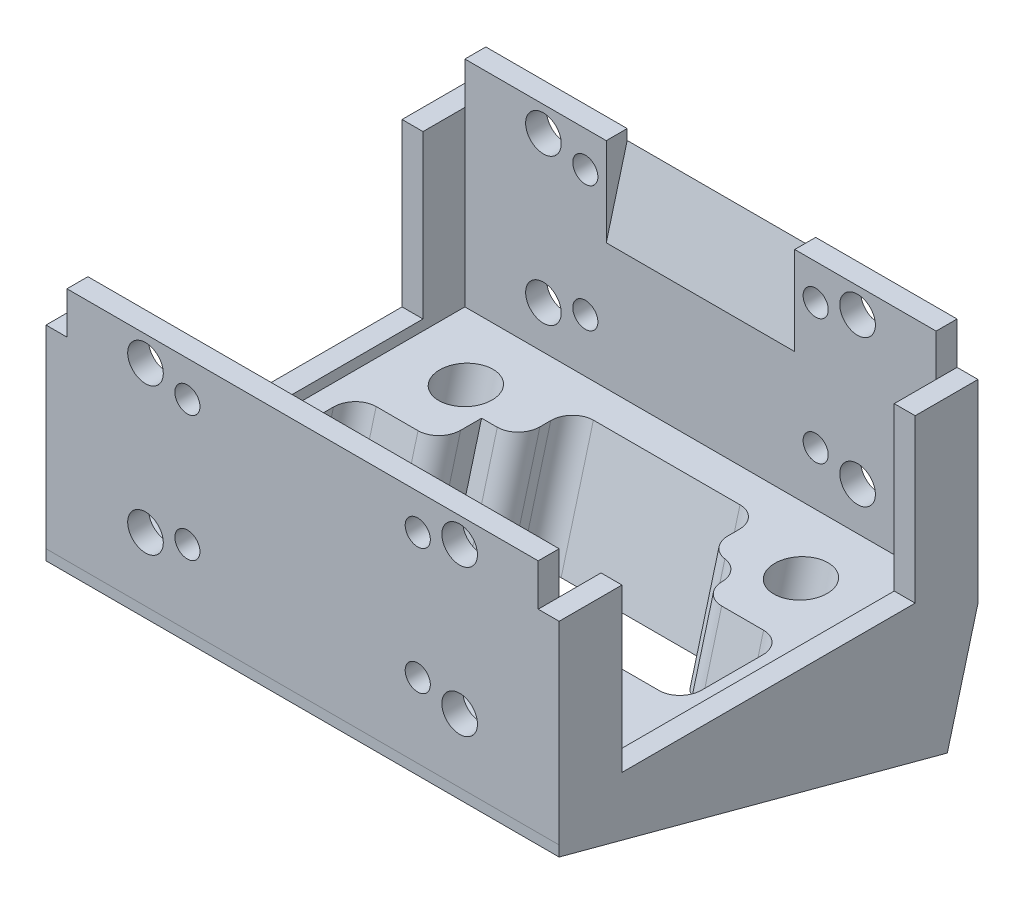
SolidWorks part; units mm, degrees
ref_plane "Front Plane" through (0, 0, 0) normal (0, 0, 1) x (1, 0, 0)
ref_plane "Top Plane" through (0, 0, 0) normal (0, 1, 0) x (1, 0, 0)
ref_plane "Right Plane" through (0, 0, 0) normal (1, 0, 0) x (0, 0, -1)
ref_plane "Plane1" through (24.5, 0, 0) normal (1, 0, 0) x (0, 0, -1)
sketch "Sketch1" plane through (24.5, 0, 0) normal (1, 0, 0) x (0, 0, -1)
  line L0 (20, 18.5) -> (-20, 18.5)
  line L1 (-20, 18.5) -> (-20, 0)
  line L2 (-20, 0) -> (-20.0017, -1)
  line L3 (-20.0017, -1) -> (17.0704, -10.9334)
  line L4 (17.0704, -10.9334) -> (20, 0)
  line L5 (20, 0) -> (20, 18.5)
extrude "Boss-Extrude1" add sketch "Sketch1" against normal blind 49
sketch "Sketch2" plane through (0, 18.5, 0) normal (0, 1, 0) x (-1, 0, 0)
  line L0 (22.5, 20) -> (22.5, 18)
  line L1 (22.5, 18) -> (-22.5, 18)
  line L2 (-22.5, 18) -> (-22.5, 20)
  line L3 (-22.5, 20) -> (22.5, 20)
extrude "Boss-Extrude2" add sketch "Sketch2" along normal blind 4
sketch "Sketch3" plane through (0, 18.5, 0) normal (0, 1, 0) x (-1, 0, 0)
  line L0 (22.5, -18) -> (22.5, -20)
  line L1 (22.5, -20) -> (-22.5, -20)
  line L2 (-22.5, -20) -> (-22.5, -18)
  line L3 (-22.5, -18) -> (22.5, -18)
extrude "Boss-Extrude3" add sketch "Sketch3" along normal blind 4
sketch "Sketch4" plane through (0, 18.5, 0) normal (0, 1, 0) x (-1, 0, 0)
  line L0 (-22.5, -18) -> (22.5, -18)
  line L1 (22.5, -18) -> (22.5, 18)
  line L2 (22.5, 18) -> (-22.5, 18)
  line L3 (-22.5, 18) -> (-22.5, -18)
extrude "Cut-Extrude1" cut sketch "Sketch4" against normal blind 16.5
sketch "Sketch5" plane through (24.5, 0, 0) normal (1, 0, 0) x (0, 0, -1)
  line L0 (-14, 18.5) -> (-14, 3)
  line L1 (-14, 3) -> (14, 3)
  line L2 (14, 3) -> (14, 18.5)
  line L3 (14, 18.5) -> (-14, 18.5)
extrude "Cut-Extrude2" cut sketch "Sketch5" against normal up to next
sketch "Sketch6" plane through (-24.5, 0, 0) normal (-1, 0, 0) x (0, 0, 1)
  line L0 (-14, 18.5) -> (-14, 3)
  line L1 (-14, 3) -> (14, 3)
  line L2 (14, 3) -> (14, 18.5)
  line L3 (14, 18.5) -> (-14, 18.5)
extrude "Cut-Extrude3" cut sketch "Sketch6" against normal through all
sketch "Sketch7" plane through (0, -5.9334, 1.5899) normal (0, -0.9659, 0.2588) x (1, 0, 0)
  line L0 (-9, -8.75) -> (-9, -13.75)
  line L1 (-9, -13.75) -> (9, -13.75)
  line L2 (9, -13.75) -> (9, -10.7187)
  line L3 (14.5, -4.8185) -> (20.5, -4.8185)
  line L4 (20.5, -4.8185) -> (20.5, 4.8185)
  line L5 (20.5, 4.8185) -> (14.4998, 4.8185)
  line L6 (9, 10.75) -> (9, 13.75)
  line L7 (9, 13.75) -> (-9, 13.75)
  line L8 (-9, 13.75) -> (-9, 10.7187)
  line L9 (-14.5, 4.8185) -> (-20.5, 4.8185)
  line L10 (-20.5, 4.8185) -> (-20.5, -4.8185)
  line L11 (-20.5, -4.8185) -> (-12.5, -4.8185)
  line L12 (-12.5, -4.8185) -> (-12.5, -8.75)
  line L13 (-12.5, -8.75) -> (-9, -8.75)
  arc A0 (9, -10.7187) -> (10.7503, -8.7344) centre (11, -10.7187) cw
  arc A1 (10.7503, -8.7344) -> (12.5003, -6.7843) centre (10.5006, -6.75) ccw
  arc A2 (12.5003, -6.7843) -> (14.5, -4.8185) centre (14.5, -6.8185) cw
  arc A3 (14.4998, 4.8185) -> (12.4999, 6.7999) centre (14.4998, 6.8185) cw
  arc A4 (12.4999, 6.7999) -> (10.75, 8.7657) centre (10.5, 6.7814) ccw
  arc A5 (10.75, 8.7657) -> (9, 10.75) centre (11, 10.75) cw
  arc A6 (-9, 10.7187) -> (-10.7503, 8.7344) centre (-11, 10.7187) cw
  arc A7 (-10.7503, 8.7344) -> (-12.5003, 6.7843) centre (-10.5006, 6.75) ccw
  arc A8 (-12.5003, 6.7843) -> (-14.5, 4.8185) centre (-14.5, 6.8185) cw
extrude "Cut-Extrude4" cut sketch "Sketch7" against normal through all
ref_plane "Plane2" through (0, 5.4116, -1.45) normal (0, 0.9659, -0.2588) x (1, 0, 0)
hole_wizard "CBORE for M2 Hex Head Machine Screw1" positions "Sketch9" profile "Sketch8" counterbore size "M2" standard "ANSI Metric"
sketch "Sketch9" plane through (0, 5.4116, -1.45) normal (0, 0.9659, -0.2588) x (1, 0, 0)
  point P0 (-16, 10.6815)
  point P1 (16, 10.6815)
sketch "Sketch8" plane through (-16, 2.647, -11.7676) normal (1, 0, 0) x (0, 0.2588, 0.9659)
  line L0 (0, 0) -> (0, 21.3402)
  line L1 (0, 21.3402) -> (1.25, 21.3402)
  line L3 (1.25, 21.3402) -> (1.25, 9.7453)
  line L4 (1.25, 9.7453) -> (2.5, 9.7453)
  line L5 (2.5, 9.7453) -> (2.5, 0)
  line L7 (2.5, 0) -> (0, 0)
  line L11 (0, -6.35) -> (0, 107.95) construction
  dimension "Thru Hole Dia." = 2.5
  dimension "Thru Hole Depth" = 21.3402
  dimension "C'Bore Dia." = 5
  dimension "C'Bore Depth" = 9.7453
ref_plane "Plane3" through (0, -0.2824, 0.0757) normal (0, 0.9659, -0.2588) x (1, 0, 0)
hole_wizard "CBORE for M2 Hex Head Machine Screw2" positions "Sketch11" profile "Sketch10" counterbore size "M2" standard "ANSI Metric"
sketch "Sketch11" plane through (0, -0.2824, 0.0757) normal (0, 0.9659, -0.2588) x (1, 0, 0)
  point P0 (-16, -11.3185)
  point P1 (16, -11.3185)
sketch "Sketch10" plane through (-16, 2.647, 11.0085) normal (1, 0, 0) x (0, 0.2588, 0.9659)
  line L0 (0, 0) -> (0, 15.4454)
  line L1 (0, 15.4454) -> (1.25, 15.4454)
  line L3 (1.25, 15.4454) -> (1.25, 3.8504)
  line L4 (1.25, 3.8504) -> (2.5, 3.8504)
  line L5 (2.5, 3.8504) -> (2.5, 0)
  line L7 (2.5, 0) -> (0, 0)
  line L11 (0, -6.35) -> (0, 107.95) construction
  dimension "Thru Hole Dia." = 2.5
  dimension "Thru Hole Depth" = 15.4454
  dimension "C'Bore Dia." = 5
  dimension "C'Bore Depth" = 3.8504
hole_wizard "Ø3.4 (3.4) Diameter Hole1" positions "Sketch13" profile "Sketch12" hole size "Ø3.4" standard "ANSI Metric"
sketch "Sketch13" plane through (0, 0, -18) normal (0, 0, 1) x (1, 0, 0)
  point P0 (15, 6.1)
  point P1 (-15, 6.1)
  point P2 (15, 20.1)
  point P3 (-15, 20.1)
sketch "Sketch12" plane through (15, 6.1, -18) normal (1, 0, 0) x (0, -1, 0)
  line L0 (0, 0) -> (0, 2)
  line L1 (0, 2) -> (1.7, 2)
  line L2 (1.7, 2) -> (1.7, 0)
  line L5 (1.7, 0) -> (0, 0)
  line L11 (0, -6.35) -> (0, 107.95) construction
  dimension "Thru Hole Dia." = 3.4
  dimension "Thru Hole Depth" = 2
hole_wizard "Ø2.4 (2.4) Diameter Hole1" positions "Sketch15" profile "Sketch14" hole size "Ø2.4" standard "ANSI Metric"
sketch "Sketch15" plane through (0, 0, -18) normal (0, 0, 1) x (1, 0, 0)
  point P0 (-11, 19.1)
  point P1 (-11, 7.1)
  point P2 (11, 19.1)
  point P3 (11, 7.1)
sketch "Sketch14" plane through (-11, 19.1, -18) normal (1, 0, 0) x (0, -1, 0)
  line L0 (0, 0) -> (0, 2)
  line L1 (0, 2) -> (1.2, 2)
  line L2 (1.2, 2) -> (1.2, 0)
  line L5 (1.2, 0) -> (0, 0)
  line L11 (0, -6.35) -> (0, 107.95) construction
  dimension "Thru Hole Dia." = 2.4
  dimension "Thru Hole Depth" = 2
hole_wizard "Ø3.4 (3.4) Diameter Hole2" positions "Sketch17" profile "Sketch16" hole size "Ø3.4" standard "ANSI Metric"
sketch "Sketch17" plane through (0, 0, 20) normal (0, 0, 1) x (1, 0, 0)
  point P0 (15, 6.1)
  point P1 (-15, 6.1)
  point P2 (15, 20.1)
  point P3 (-15, 20.1)
sketch "Sketch16" plane through (15, 6.1, 20) normal (1, 0, 0) x (0, -1, 0)
  line L0 (0, 0) -> (0, 40)
  line L1 (0, 40) -> (1.7, 40)
  line L2 (1.7, 40) -> (1.7, 0)
  line L5 (1.7, 0) -> (0, 0)
  line L11 (0, -6.35) -> (0, 107.95) construction
  dimension "Thru Hole Dia." = 3.4
  dimension "Thru Hole Depth" = 40
hole_wizard "Ø2.4 (2.4) Diameter Hole2" positions "Sketch19" profile "Sketch18" hole size "Ø2.4" standard "ANSI Metric"
sketch "Sketch19" plane through (0, 0, 20) normal (0, 0, 1) x (1, 0, 0)
  point P0 (-11, 19.1)
  point P1 (-11, 7.1)
  point P2 (11, 19.1)
  point P3 (11, 7.1)
sketch "Sketch18" plane through (-11, 19.1, 20) normal (1, 0, 0) x (0, -1, 0)
  line L0 (0, 0) -> (0, 40)
  line L1 (0, 40) -> (1.2, 40)
  line L2 (1.2, 40) -> (1.2, 0)
  line L5 (1.2, 0) -> (0, 0)
  line L11 (0, -6.35) -> (0, 107.95) construction
  dimension "Thru Hole Dia." = 2.4
  dimension "Thru Hole Depth" = 40
fillet "Fillet1" radius 2 10 edges at (-9, -3.0991, -8.2283) (20.5, -1.3432, 5.3484) (-20.5, -2.5903, -4.2944) (9, -3.7461, -13.2313) (-20.5, -1.3432, 5.3484) (20.5, -2.5903, -4.2944) (-9, -0.1873, 14.2852) (-9, -3.7461, -13.2313) (9, -0.1873, 14.2852) (-12.5, -2.5903, -4.2944)
